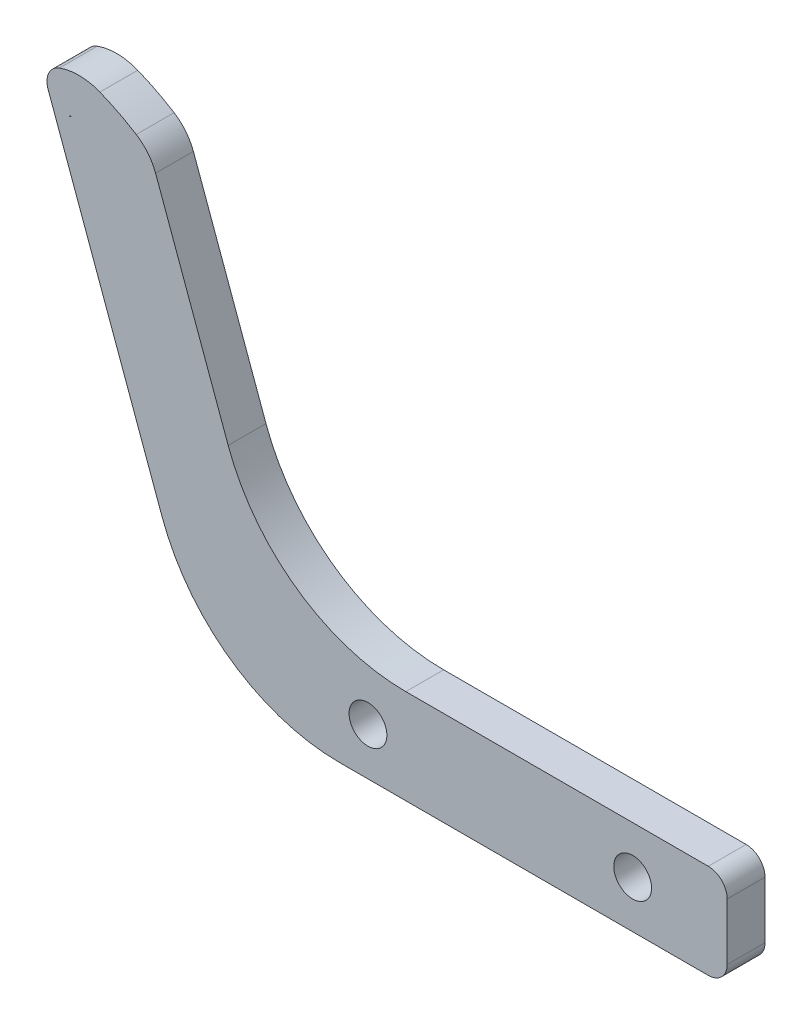
SolidWorks part; units mm, degrees
material "Thornel Mat VMA"
ref_plane "前视基准面" through (0, 0, 0) normal (0, 0, 1) x (1, 0, 0)
ref_plane "上视基准面" through (0, 0, 0) normal (0, 1, 0) x (1, 0, 0)
ref_plane "右视基准面" through (0, 0, 0) normal (1, 0, 0) x (0, 0, -1)
sketch "草图1" plane through (0, 0, 0) normal (0, 0, 1) x (1, 0, 0)
  line L0 (-61.8446, 41.2803) -> (-45, -5)
  line L1 (-45, -5) -> (5, -5)
  line L2 (-45, -5) -> (-45, 5)
  line L3 (-45, 5) -> (5, 5)
  line L4 (5, -5) -> (5, 5)
  line L5 (-61.8446, 41.2803) -> (-49.9686, 37.8892)
  line L6 (-49.9686, 37.8892) -> (-37.9979, 5)
  line L8 (5, 5) -> (10, 5)
  line L9 (5, 5) -> (5, -5)
  line L10 (5, -5) -> (10, -5)
  line L11 (10, 5) -> (10, -5)
  circle A0 centre (0, 0) radius 2
  circle A1 centre (-28, 0) radius 2
  point P10 (-45, 0)
  dimension "D2" = 4
  dimension "D1" = 28
  dimension "D3" = 5
  dimension "D4" = 10
  dimension "D5" = 50
  dimension "D6" = 110
  dimension "D7" = 40
  dimension "D8" = 10
  dimension "D9" = 35
  dimension "D10" = 5
extrude "凸台-拉伸1" add sketch "草图1" along normal blind 4
fillet "圆角1" radius 20 2 edges at (-45, -5, 2) (-37.9979, 5, 2)
fillet "圆角2" radius 20 1 edges at (-49.9686, 37.8892, 2)
fillet "圆角3" radius 2 3 edges at (-61.8446, 41.2803, 2) (10, -5, 2) (10, 5, 2)
sketch "草图2" plane through (0, 0, 4) normal (0, 0, 1) x (1, 0, 0)
  line L0 (-64.2228, 36.1191) -> (-53.5485, 6.7915)
  line L1 (-30.9958, -9) -> (8, -9)
  line L2 (14, -3) -> (14, 3)
  line L3 (8, 9) -> (-23.9938, 9)
  line L4 (-39.0289, 19.5277) -> (-42.7197, 29.6681)
  line L5 (-30.9958, -5) -> (8, -5)
  line L6 (10, -3) -> (10, 3)
  line L7 (8, 5) -> (-23.9938, 5)
  line L8 (-42.7876, 18.1596) -> (-46.4785, 28.3001)
  line L9 (-60.4641, 37.4872) -> (-49.7897, 8.1596)
  line L10 (-30.9958, -5) -> (8, -5)
  line L11 (10, -3) -> (10, 3)
  line L12 (8, 5) -> (-23.9938, 5)
  line L13 (-42.7876, 18.1596) -> (-46.4785, 28.3001)
  line L14 (-60.4641, 37.4872) -> (-49.7897, 8.1596)
  line L15 (-60.4641, 37.4872) -> (-61.8321, 41.2459)
  line L16 (-46.4785, 28.3001) -> (-50.4671, 39.2587)
  arc A0 (-42.7197, 29.6681) -> (-56.3555, 43.7417) centre (-65.2723, 21.4597) ccw
  arc A1 (-56.3555, 43.7417) -> (-64.2228, 36.1191) centre (-58.5847, 38.1712) ccw
  arc A2 (-53.5485, 6.7915) -> (-30.9958, -9) centre (-30.9958, 15) ccw
  arc A3 (8, -9) -> (14, -3) centre (8, -3) ccw
  arc A4 (14, 3) -> (8, 9) centre (8, 3) ccw
  arc A5 (-39.0289, 19.5277) -> (-23.9938, 9) centre (-23.9938, 25) ccw
  arc A6 (8, -5) -> (10, -3) centre (8, -3) ccw
  arc A7 (10, 3) -> (8, 5) centre (8, 3) ccw
  arc A8 (-42.7876, 18.1596) -> (-23.9938, 5) centre (-23.9938, 25) ccw
  arc A9 (-46.4785, 28.3001) -> (-57.8416, 40.028) centre (-65.2723, 21.4597) ccw
  arc A10 (-57.8416, 40.028) -> (-60.4641, 37.4872) centre (-58.5847, 38.1712) ccw
  arc A11 (-49.7897, 8.1596) -> (-30.9958, -5) centre (-30.9958, 15) ccw
  arc A12 (8, -5) -> (10, -3) centre (8, -3) ccw
  arc A13 (10, 3) -> (8, 5) centre (8, 3) ccw
  arc A14 (-42.7876, 18.1596) -> (-23.9938, 5) centre (-23.9938, 25) ccw
  arc A15 (-46.4785, 28.3001) -> (-57.8416, 40.028) centre (-65.2723, 21.4597) ccw
  arc A16 (-57.8416, 40.028) -> (-60.4641, 37.4872) centre (-58.5847, 38.1712) ccw
  arc A17 (-49.7897, 8.1596) -> (-30.9958, -5) centre (-30.9958, 15) ccw
  circle A18 centre (-59.9528, 41.93) radius 2
  circle A19 centre (-55.1655, 37.5486) radius 5
  point P40 (0, 0)
  arc M21 (-46.4785, 28.3001) -> (-57.8416, 40.028) centre (-65.2723, 21.4597) ccw
  arc M22 (-57.8416, 40.028) -> (-60.4641, 37.4872) centre (-58.5847, 38.1712) ccw
  dimension "D3" = 4
  dimension "D4" = 10
  dimension "D1" = 0
  dimension "D2" = 4
extrude "凸台-拉伸2" add sketch "草图2" against normal blind 4 contours A19 A18 L15 M22 | A19 A18 | A19 A0 A1 A18 | A19 A18 A15 M22 | A18 A19 | A19 L16 M21
